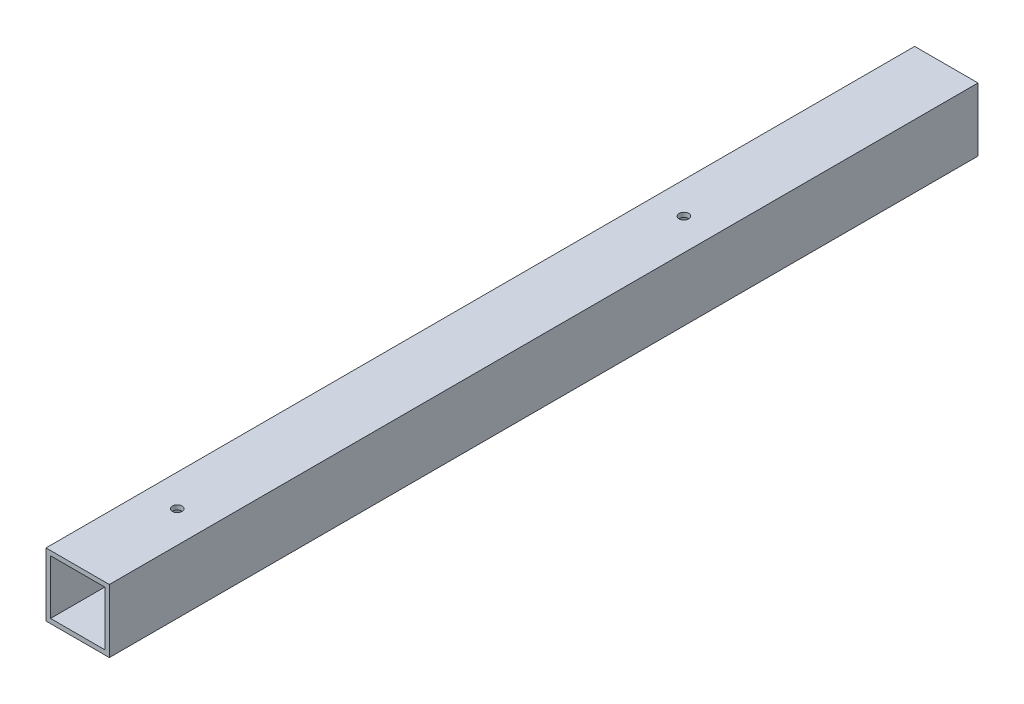
SolidWorks part; units mm, degrees
material "6063-T6"
ref_plane "Front Plane" through (0, 0, 0) normal (0, 0, 1) x (1, 0, 0)
ref_plane "Top Plane" through (0, 0, 0) normal (0, 1, 0) x (1, 0, 0)
ref_plane "Right Plane" through (0, 0, 0) normal (1, 0, 0) x (0, 0, -1)
sketch "Sketch1" plane through (0, 0, 0) normal (0, 0, 1) x (1, 0, 0)
  line L0 (3.175, 3.175) -> (3.175, 41.275)
  line L1 (0, 0) -> (44.45, 0)
  line L2 (0, 0) -> (0, 44.45)
  line L3 (0, 44.45) -> (44.45, 44.45)
  line L4 (44.45, 0) -> (44.45, 44.45)
  line L5 (3.175, 41.275) -> (41.275, 41.275)
  line L6 (41.275, 3.175) -> (41.275, 41.275)
  line L7 (3.175, 3.175) -> (41.275, 3.175)
  dimension "D2" = 44.45
  dimension "D1" = 3.175
extrude "Boss-Extrude1" add sketch "Sketch1" along normal blind 609.6
hole_wizard "1/4 Clearance Hole1" positions "Sketch2" profile "Sketch3" hole size "1/4" standard "ANSI Inch" end condition through all
sketch "Sketch2" plane through (0, 44.45, 0) normal (0, 1, 0) x (1, 0, 0)
  line L0 (44.45, 0) -> (0, 0) construction
  line L1 (44.45, -609.6) -> (0, -609.6) construction
  point P0 (22.225, -539.75)
  point P2 (22.225, -184.15)
  point P9 (22.225, -609.6)
  dimension "D1" = 184.15
  dimension "D2" = 355.6
sketch "Sketch3" plane through (22.225, 44.45, 539.75) normal (1, 0, 0) x (0, 0, 1)
  line L0 (0, 0) -> (0, 44.45)
  line L1 (0, 44.45) -> (3.3782, 44.45)
  line L2 (3.3782, 44.45) -> (3.3782, 0)
  line L5 (3.3782, 0) -> (0, 0)
  line L11 (0, -6.35) -> (0, 107.95) construction
  dimension "Thru Hole Dia." = 6.7564
  dimension "Thru Hole Depth" = 44.45
